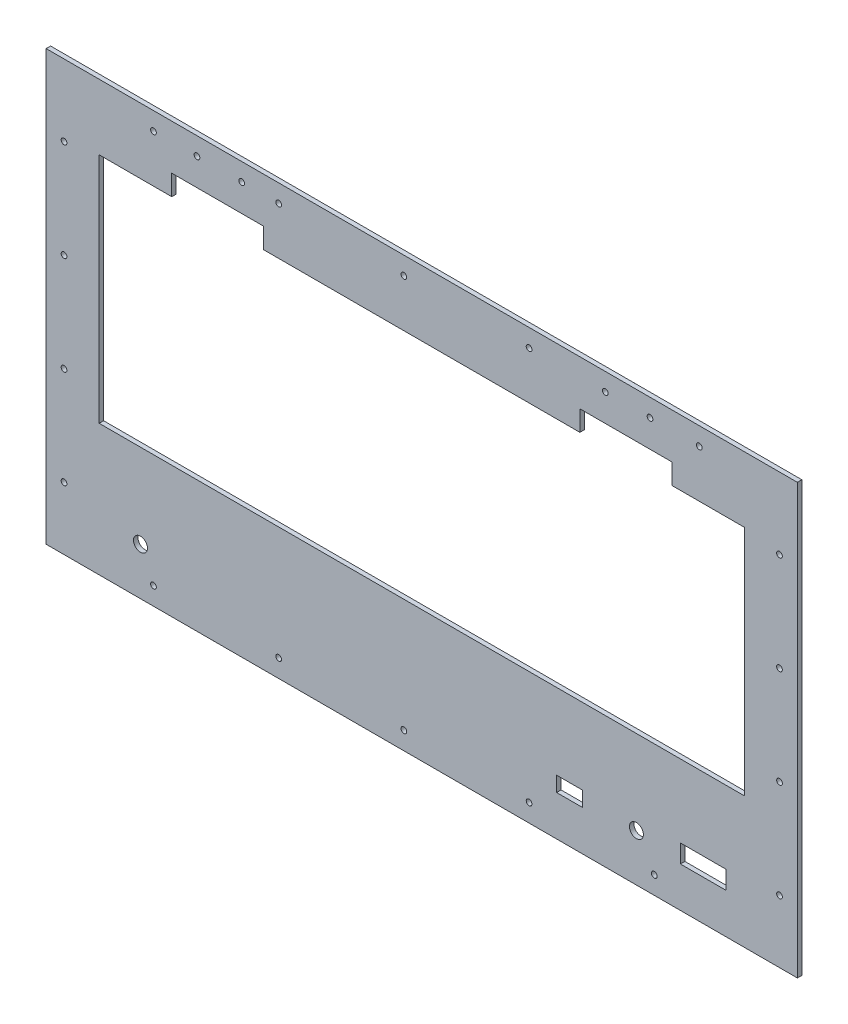
SolidWorks part; units mm, degrees
ref_plane "Front Plane" through (0, 0, 0) normal (0, 0, 1) x (1, 0, 0)
ref_plane "Top Plane" through (0, 0, 0) normal (0, 1, 0) x (1, 0, 0)
ref_plane "Right Plane" through (0, 0, 0) normal (1, 0, 0) x (0, 0, -1)
sketch "Sketch1" plane through (0, 0, 0) normal (0, 0, 1) x (1, 0, 0)
  line L1 (533.4, 0) -> (0, 0)
  line L2 (533.4, 0) -> (533.4, 304.8)
  line L3 (533.4, 304.8) -> (0, 304.8)
  line L4 (0, 0) -> (0, 304.8)
  dimension "D1" = 533.4
  dimension "D2" = 304.8
extrude "Boss-Extrude1" add sketch "Sketch1" along normal blind 3.175
sketch "Sketch5" plane through (0, 0, 3.175) normal (0, 0, 1) x (1, 0, 0)
  line L0 (0, 304.8) -> (0, 0) construction
  line L1 (0, 0) -> (533.4, 0) construction
  line L2 (0, 152.4) -> (533.4, 152.4) construction
  line L3 (533.4, 0) -> (533.4, 304.8) construction
  line L4 (533.4, 304.8) -> (0, 304.8) construction
  circle A0 centre (76.2, 12.7) radius 2.032
  circle A1 centre (165.1, 12.7) radius 2.032
  circle A2 centre (254, 12.7) radius 2.032
  circle A3 centre (342.9, 12.7) radius 2.032
  circle A4 centre (431.8, 12.7) radius 2.032
  circle A8 centre (342.9, 292.1) radius 2.032
  circle A9 centre (254, 292.1) radius 2.032
  circle A10 centre (165.1, 292.1) radius 2.032
  circle A11 centre (76.2, 292.1) radius 2.032
  circle A12 centre (463.7195, 292.1) radius 2.032
  circle A13 centre (520.7, 12.7) radius 2.032 [skipped]
  dimension "D1" = 4.064
  dimension "D2" = 76.2
  dimension "D5" = 88.9
  dimension "D7" = 4.064
  dimension "D6" = 69.6805
  dimension "D8" = 12.7
  dimension "D4" = 12.7
  dimension "D3" = 6
extrude "Cut-Extrude4" cut sketch "Sketch5" against normal through all
sketch "Sketch6" plane through (0, 0, 3.175) normal (0, 0, 1) x (1, 0, 0)
  line L0 (0, 304.8) -> (0, 0) construction
  line L1 (533.4, 304.8) -> (0, 304.8) construction
  line L2 (266.7, 304.8) -> (266.7, 0) construction
  line L3 (0, 0) -> (533.4, 0) construction
  circle A0 centre (12.7, 254) radius 2.032
  circle A1 centre (12.7, 184.15) radius 2.032
  circle A2 centre (12.7, 114.3) radius 2.032
  circle A3 centre (12.7, 44.45) radius 2.032
  circle A4 centre (520.7, 44.45) radius 2.032
  circle A5 centre (520.7, 114.3) radius 2.032
  circle A6 centre (520.7, 184.15) radius 2.032
  circle A7 centre (520.7, 254) radius 2.032
  dimension "D1" = 4.064
  dimension "D3" = 50.8
  dimension "D5" = 69.85
  dimension "D2" = 12.7
  dimension "D4" = 4
extrude "Cut-Extrude5" cut sketch "Sketch6" against normal blind 3.175
sketch "Sketch7" plane through (0, 0, 0) normal (0, 0, -1) x (-1, 0, 0)
  line L0 (-533.4, 304.8) -> (0, 304.8) construction
  line L1 (-266.7, 304.8) -> (-266.7, 0) construction
  line L2 (0, 0) -> (-533.4, 0) construction
  line L3 (-397.0242, 266.7829) -> (-397.0242, 304.8) construction
  line L4 (-428.7742, 266.7829) -> (-428.7742, 304.8) construction
  circle A0 centre (-138.858, 292.1829) radius 2.032
  circle A1 centre (-107.108, 292.1829) radius 2.032
  circle A2 centre (-76.2, 292.1) radius 2.032 construction
  circle A3 centre (-428.7742, 292.1829) radius 2.032
  circle A4 centre (-397.0242, 292.1829) radius 2.032
  dimension "D1" = 4.064
  dimension "D2" = 4.064
  dimension "D5" = 31.75
  dimension "D6" = 12.6171
  dimension "D7" = 31.75
  dimension "D8" = 4.064
  dimension "D9" = 4.064
  dimension "D10" = 12.6171
  dimension "D3" = 12.6171
  dimension "D4" = 30.908
extrude "Cut-Extrude6" cut sketch "Sketch7" against normal through all
sketch "Sketch8" plane through (0, 0, 3.175) normal (0, 0, 1) x (1, 0, 0)
  line L0 (533.4, 0) -> (533.4, 304.8) construction
  line L1 (37.6142, 258.306) -> (495.808, 258.306)
  line L2 (37.6142, 258.306) -> (37.6142, 93.206)
  line L3 (37.6142, 93.206) -> (495.808, 93.206)
  line L4 (495.808, 258.306) -> (495.808, 93.206)
  line L5 (89.1762, 272.784) -> (154.4542, 272.784)
  line L6 (89.1762, 272.784) -> (89.1762, 258.306)
  line L7 (89.1762, 258.306) -> (154.4542, 258.306)
  line L8 (154.4542, 272.784) -> (154.4542, 258.306)
  line L9 (266.7111, 258.306) -> (266.7111, 93.206) construction
  line L10 (0, 304.8) -> (0, 0) construction
  line L11 (533.4, 304.8) -> (0, 304.8) construction
  line L12 (444.246, 258.306) -> (378.968, 258.306)
  line L13 (378.968, 272.784) -> (378.968, 258.306)
  line L14 (444.246, 272.784) -> (378.968, 272.784)
  line L15 (444.246, 272.784) -> (444.246, 258.306)
  dimension "D1" = 37.6142
  dimension "D2" = 37.592
  dimension "D3" = 165.1
  dimension "D4" = 14.478
  dimension "D5" = 65.278
  dimension "D6" = 51.562
  dimension "D7" = 32.016
extrude "Cut-Extrude7" cut sketch "Sketch8" against normal through all contours L4 L1 L2 L3 | L8 L5 L6 L1 | L12 L13 L14 L15
sketch "Sketch9" plane through (0, 0, 3.175) normal (0, 0, 1) x (1, 0, 0)
  line L0 (0, 12.7) -> (533.4, 12.7) construction
  line L1 (533.4, 0) -> (533.4, 304.8) construction
  line L2 (0, 304.8) -> (0, 0) construction
  line L3 (0, 28.575) -> (533.4, 28.575) construction
  line L5 (450.342, 28.575) -> (482.6, 28.575)
  line L6 (450.342, 28.575) -> (450.342, 41.529)
  line L7 (450.342, 41.529) -> (482.6, 41.529)
  line L8 (482.6, 28.575) -> (482.6, 41.529)
  line L13 (362.458, 28.575) -> (381, 28.575)
  line L14 (362.458, 28.575) -> (362.458, 39.243)
  line L15 (362.458, 39.243) -> (381, 39.243)
  line L16 (381, 28.575) -> (381, 39.243)
  circle A0 centre (419.1, 33.528) radius 4.953
  circle A1 centre (66.9778, 33.528) radius 4.953
  point P6 (266.7, 12.7)
  dimension "D2" = 9.906
  dimension "D8" = 9.906
  dimension "D1" = 15.875
  dimension "D3" = 114.3
  dimension "D4" = 12.954
  dimension "D5" = 32.258
  dimension "D6" = 50.8
  dimension "D9" = 10.668
  dimension "D10" = 18.542
  dimension "D11" = 152.4
  dimension "D7" = 466.4222
  dimension "D12" = 4.953
extrude "Cut-Extrude8" cut sketch "Sketch9" against normal through all
sketch "Sketch10" plane through (0, 0, 3.175) normal (0, 0, 1) x (1, 0, 0)
equation "\"D1@Sketch9\"=.5in + 1/8in"
